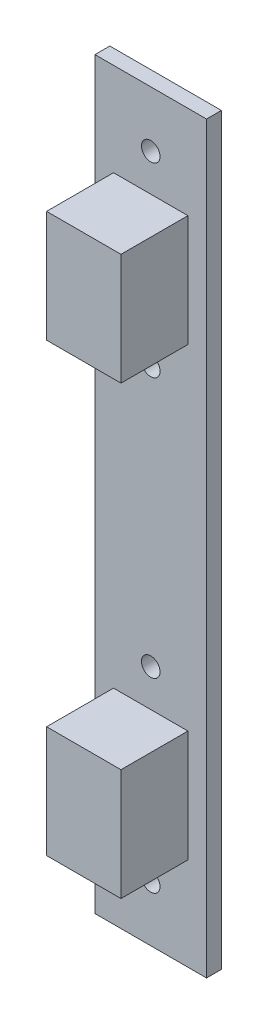
SolidWorks part; units mm, degrees
ref_plane "Alzado" through (0, 0, 0) normal (0, 0, 1) x (1, 0, 0)
ref_plane "Planta" through (0, 0, 0) normal (0, 1, 0) x (1, 0, 0)
ref_plane "Vista lateral" through (0, 0, 0) normal (1, 0, 0) x (0, 0, -1)
sketch "Croquis1" plane through (0, 0, 0) normal (0, 0, 1) x (1, 0, 0)
  line L0 (0, 50) -> (0, 42.5) construction
  line L1 (-7.5, -50) -> (7.5, -50)
  line L2 (-7.5, -50) -> (-7.5, 50)
  line L3 (-7.5, 50) -> (7.5, 50)
  line L4 (7.5, -50) -> (7.5, 50)
  line L5 (-7.5, -50) -> (7.5, 50) construction
  line L6 (-7.5, 50) -> (7.5, -50) construction
  line L7 (0, 42.5) -> (0, 17.5) construction
  line L8 (7.5, 0) -> (-7.5, 0) construction
  circle A0 centre (0, 42.5) radius 1.25
  circle A1 centre (0, 17.5) radius 1.25
  circle A2 centre (0, -42.5) radius 1.25
  circle A3 centre (0, -17.5) radius 1.25
  point P0 (0, 0)
extrude "Saliente-Extruir1" add sketch "Croquis1" against normal blind 2 contours L2 L1 L4 L3
sketch "Croquis2" plane through (0, 0, 0) normal (0, 0, 1) x (1, 0, 0)
  line L0 (0, 17.5) -> (0, 42.5) construction
  line L1 (0, 0) -> (7.5, 0) construction
  line L2 (-5, 22.5) -> (5, 22.5)
  line L3 (-5, 22.5) -> (-5, 37.5)
  line L4 (-5, 37.5) -> (5, 37.5)
  line L5 (5, 22.5) -> (5, 37.5)
  line L6 (-5, 22.5) -> (5, 37.5) construction
  line L7 (-5, 37.5) -> (5, 22.5) construction
  line L8 (7.5, -50) -> (7.5, 50) construction
  line L9 (-5, -37.5) -> (5, -37.5)
  line L10 (5, -22.5) -> (5, -37.5)
  line L11 (-5, -22.5) -> (5, -22.5)
  line L12 (-5, -22.5) -> (-5, -37.5)
  point P4 (0, 30)
extrude "Saliente-Extruir2" add sketch "Croquis2" along normal blind 9
